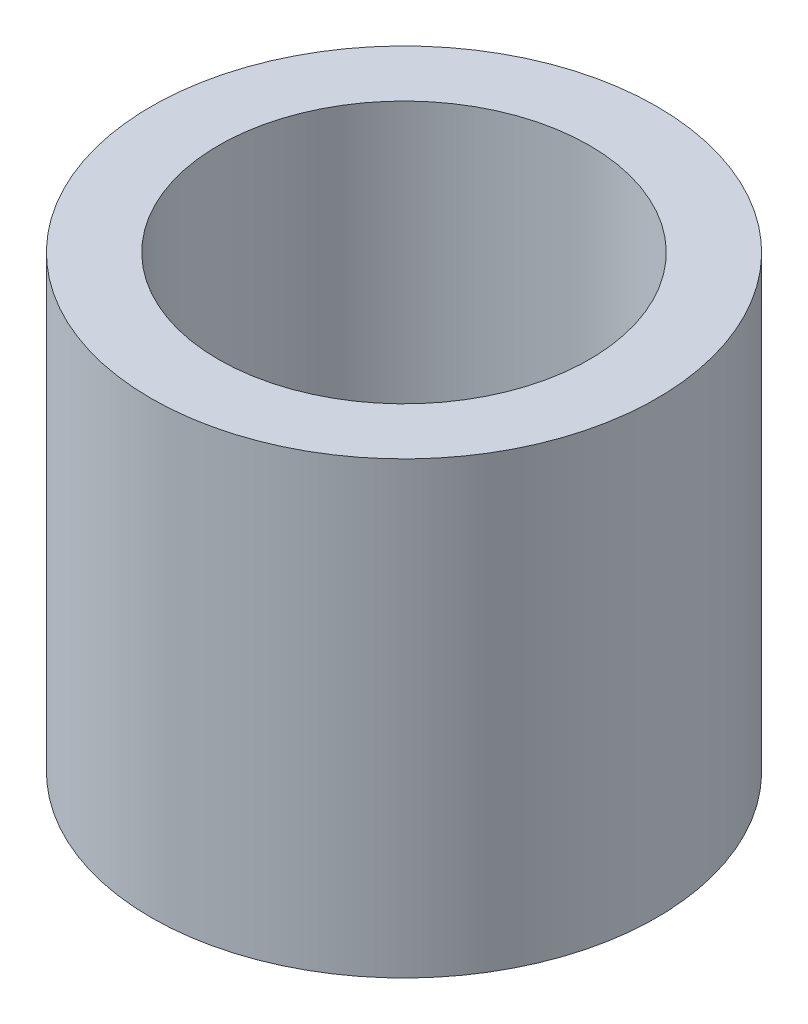
SolidWorks part; units mm, degrees
material "Markforged"
ref_plane "Front Plane" through (0, 0, 0) normal (0, 0, 1) x (1, 0, 0)
ref_plane "Top Plane" through (0, 0, 0) normal (0, 1, 0) x (1, 0, 0)
ref_plane "Right Plane" through (0, 0, 0) normal (1, 0, 0) x (0, 0, -1)
other "Bounding Box"
ref_plane "Default Plane" through (-8.9266, -12.7485, 0) normal (-0.1736, 0.9848, 0) x (0.9848, 0.1736, 0)
sketch "Sketch1" plane through (0, 0, 0) normal (0, 1, 0) x (1, 0, 0)
  circle A0 centre (0, 0) radius 4.191
  circle A1 centre (0, 0) radius 5.715
  dimension "D1" = 8.382
  dimension "D2" = 11.43
extrude "Boss-Extrude1" add sketch "Sketch1" along normal mid plane 10.16
